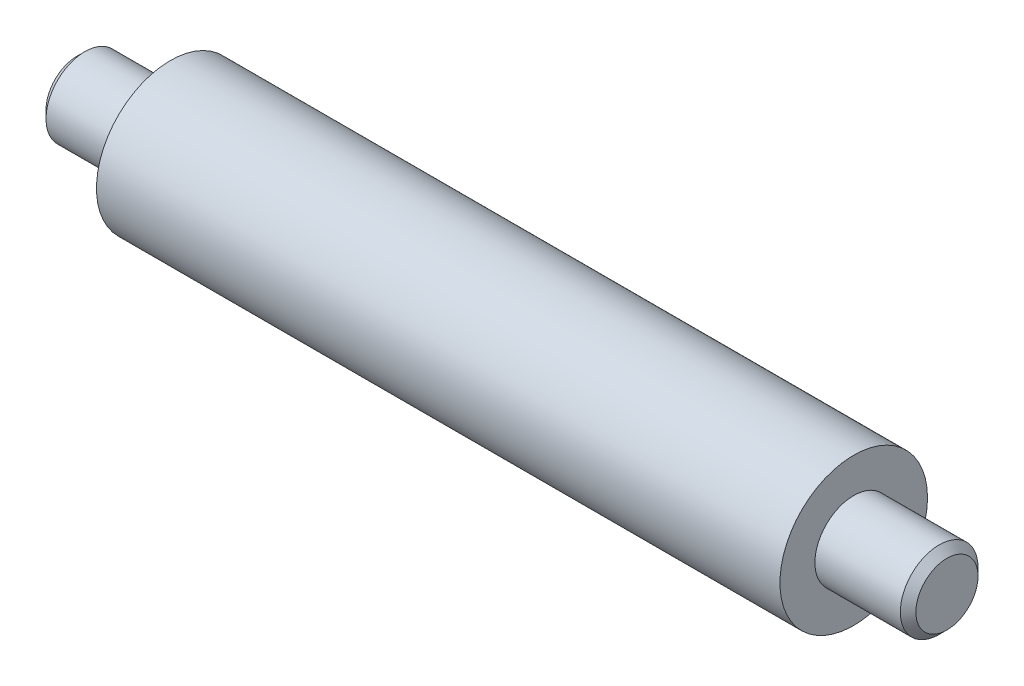
SolidWorks part; units mm, degrees
ref_plane "Front Plane" through (0, 0, 0) normal (0, 0, 1) x (1, 0, 0)
ref_plane "Top Plane" through (0, 0, 0) normal (0, 1, 0) x (1, 0, 0)
ref_plane "Right Plane" through (0, 0, 0) normal (1, 0, 0) x (0, 0, -1)
sketch "Sketch1" plane through (0, 0, 0) normal (1, 0, 0) x (0, 0, -1)
  circle A0 centre (0, 0) radius 47.5
  dimension "D1" = 95
extrude "Boss-Extrude1" add sketch "Sketch1" along normal mid plane 440
sketch "Sketch2" plane through (0, 0, 0) normal (1, 0, 0) x (0, 0, -1)
  circle A0 centre (0, 0) radius 25
  dimension "D1" = 50
extrude "Boss-Extrude2" add sketch "Sketch2" along normal mid plane 560
chamfer "Chamfer1" distance 5 angle 45 2 edges at (-280, 0, -25) (280, 0, -25)
